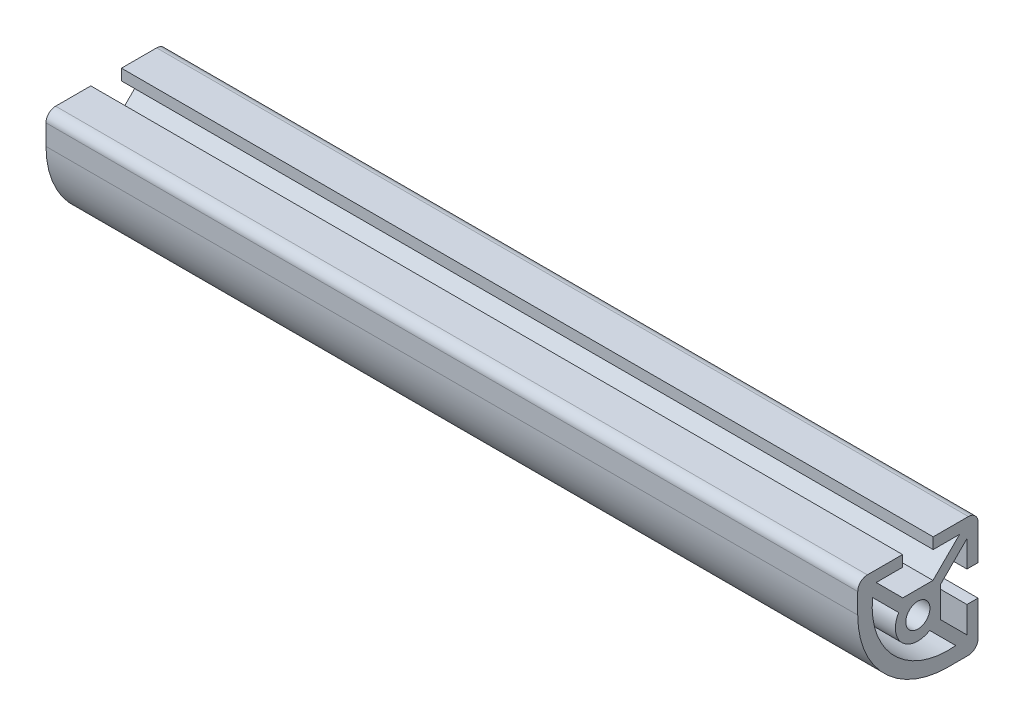
SolidWorks part; units mm, degrees
ref_plane "Front Plane" through (0, 0, 0) normal (0, 0, 1) x (1, 0, 0)
ref_plane "Top Plane" through (0, 0, 0) normal (0, 1, 0) x (1, 0, 0)
ref_plane "Right Plane" through (0, 0, 0) normal (1, 0, 0) x (0, 0, -1)
sketch "Sketch1" plane through (0, 0, 0) normal (1, 0, 0) x (0, 0, -1)
  line L0 (8.0038, -9.5663) -> (2.4852, -4.0478) construction
  line L1 (-4.0478, 2.4852) -> (-9.5663, 8.0038) construction
  line L2 (-3.1872, 4.7498) -> (-8.8006, 10.3632) construction
  line L3 (-8.8006, 10.3632) -> (-3.2385, 10.3632) construction
  line L4 (-3.2385, 10.3632) -> (-3.2385, 12.7) construction
  line L5 (-3.2385, 12.7) -> (-10.668, 12.7) construction
  line L6 (-12.7, 10.668) -> (-12.7, 6.35) construction
  line L7 (6.35, -12.7) -> (10.668, -12.7) construction
  line L8 (12.7, -10.668) -> (12.7, -3.2385) construction
  line L9 (12.7, -3.2385) -> (10.3632, -3.2385) construction
  line L10 (10.3632, -3.2385) -> (10.3632, -8.8006) construction
  line L11 (10.3632, -8.8006) -> (4.7498, -3.1872) construction
  line L12 (4.7498, -3.1872) -> (4.7498, 3.1872) construction
  line L13 (4.7498, 3.1872) -> (10.3632, 8.8006) construction
  line L14 (10.3632, 8.8006) -> (10.3632, 3.2385) construction
  line L15 (10.3632, 3.2385) -> (12.7, 3.2385) construction
  line L16 (12.7, 3.2385) -> (12.7, 10.668) construction
  line L17 (10.668, 12.7) -> (3.2385, 12.7) construction
  line L18 (3.2385, 12.7) -> (3.2385, 10.3632) construction
  line L19 (3.2385, 10.3632) -> (8.8006, 10.3632) construction
  line L20 (8.8006, 10.3632) -> (3.1872, 4.7498) construction
  line L21 (3.1872, 4.7498) -> (-3.1872, 4.7498) construction
  line L22 (-12.7, 0) -> (12.7, 0) construction
  line L23 (0, -12.7) -> (0, 12.7) construction
  line L24 (-7.1204, -7.1204) -> (-4.9651, -4.9651) construction
  line L25 (11.5316, -3.2385) -> (11.5316, 3.2385) construction
  line L26 (-3.2385, 11.5316) -> (3.2385, 11.5316) construction
  line L27 (11.5316, 0) -> (4.7498, 0) construction
  line L28 (0, 11.5316) -> (0, 4.7498) construction
  line L29 (-9.5663, 8.0038) -> (-8.0038, 9.5663) construction
  line L30 (3.1872, 4.7498) -> (4.7498, 3.1872) construction
  circle A0 centre (0, 0) radius 2.5527 construction
  arc A1 (-10.668, 12.7) -> (-12.7, 10.668) centre (-10.668, 10.668) ccw construction
  arc A2 (-12.7, 6.35) -> (6.35, -12.7) centre (6.35, 6.35) ccw construction
  arc A4 (12.7, 10.668) -> (10.668, 12.7) centre (10.668, 10.668) ccw construction
  arc A5 (-4.0478, 2.4852) -> (2.4852, -4.0478) centre (0, 0) ccw construction
  arc A6 (-9.5663, 8.0038) -> (8.0038, -9.5663) centre (6.35, 6.35) ccw construction
  arc A7 (12.7, -10.668) -> (10.668, -12.7) centre (10.668, -10.668) cw construction
  dimension "Radius" = 19.05
  dimension "Corner Radius" = 2.032
  dimension "Center Diameter" = 5.1054
  dimension "Rail Width" = 25.4
  dimension "Outer Thickness" = 2.3368
  dimension "Radius Thickness" = 3.048
  dimension "Leg Thickness" = 2.2098
  dimension "Rail Height" = 25.4
  dimension "TSlot Width" = 6.477
  dimension "TSlot Depth" = 7.9502
sketch "Sketch2" plane through (0, 0, 0) normal (0, 0, 1) x (1, 0, 0)
  line L0 (-85.725, 0) -> (85.725, 0) construction
  point P2 (-34.925, 0)
  point P4 (34.925, 0)
  dimension "Length" = 171.45
  dimension "D1" = 50.8
  dimension "D2" = 50.8
sketch "Sketch3" plane through (0, 0, 0) normal (1, 0, 0) x (0, 0, -1)
  line L0 (-10.668, 12.7) -> (-3.2385, 12.7)
  line L1 (-3.2385, 12.7) -> (-3.2385, 10.3632)
  line L2 (-3.2385, 10.3632) -> (-8.8006, 10.3632)
  line L3 (-8.8006, 10.3632) -> (-3.1872, 4.7498)
  line L4 (-3.1872, 4.7498) -> (3.1872, 4.7498)
  line L5 (3.1872, 4.7498) -> (8.8006, 10.3632)
  line L6 (8.8006, 10.3632) -> (3.2385, 10.3632)
  line L7 (3.2385, 10.3632) -> (3.2385, 12.7)
  line L8 (3.2385, 12.7) -> (10.668, 12.7)
  line L9 (12.7, 10.668) -> (12.7, 3.2385)
  line L10 (12.7, 3.2385) -> (10.3632, 3.2385)
  line L11 (10.3632, 3.2385) -> (10.3632, 8.8006)
  line L12 (10.3632, 8.8006) -> (4.7498, 3.1872)
  line L13 (4.7498, 3.1872) -> (4.7498, -3.1872)
  line L14 (4.7498, -3.1872) -> (10.3632, -8.8006)
  line L15 (10.3632, -8.8006) -> (10.3632, -3.2385)
  line L16 (10.3632, -3.2385) -> (12.7, -3.2385)
  line L17 (12.7, -3.2385) -> (12.7, -10.668)
  line L18 (2.4852, -4.0478) -> (8.0038, -9.5663)
  line L19 (10.668, -12.7) -> (6.35, -12.7)
  line L20 (-9.5663, 8.0038) -> (-4.0478, 2.4852)
  line L21 (-12.7, 10.668) -> (-12.7, 6.35)
  arc A0 (-12.7, 10.668) -> (-10.668, 12.7) centre (-10.668, 10.668) cw
  arc A1 (10.668, 12.7) -> (12.7, 10.668) centre (10.668, 10.668) cw
  arc A2 (12.7, -10.668) -> (10.668, -12.7) centre (10.668, -10.668) cw
  arc A3 (-12.7, 6.35) -> (6.35, -12.7) centre (6.35, 6.35) ccw
  arc A4 (-4.0478, 2.4852) -> (2.4852, -4.0478) centre (0, 0) ccw
  arc A7 (-4.0478, 2.4852) -> (2.4852, -4.0478) centre (0, 0) ccw construction
  arc A8 (-9.5663, 8.0038) -> (8.0038, -9.5663) centre (6.35, 6.35) ccw
  circle A9 centre (0, 0) radius 2.5527
  circle A10 centre (0, 0) radius 2.5527 construction
extrude "Boss-Extrude1" add sketch "Sketch3" along normal up to vertex (85.725 mm away) and the other way up to vertex (85.725 mm away) up to point (85.725, 0, 0) other way up to point (-85.725, 0, 0)
equation "\"D1@Sketch2\"=\"Rail Width@Sketch1\"*2"
equation "\"D2@Sketch2\"=\"D1@Sketch2\""
